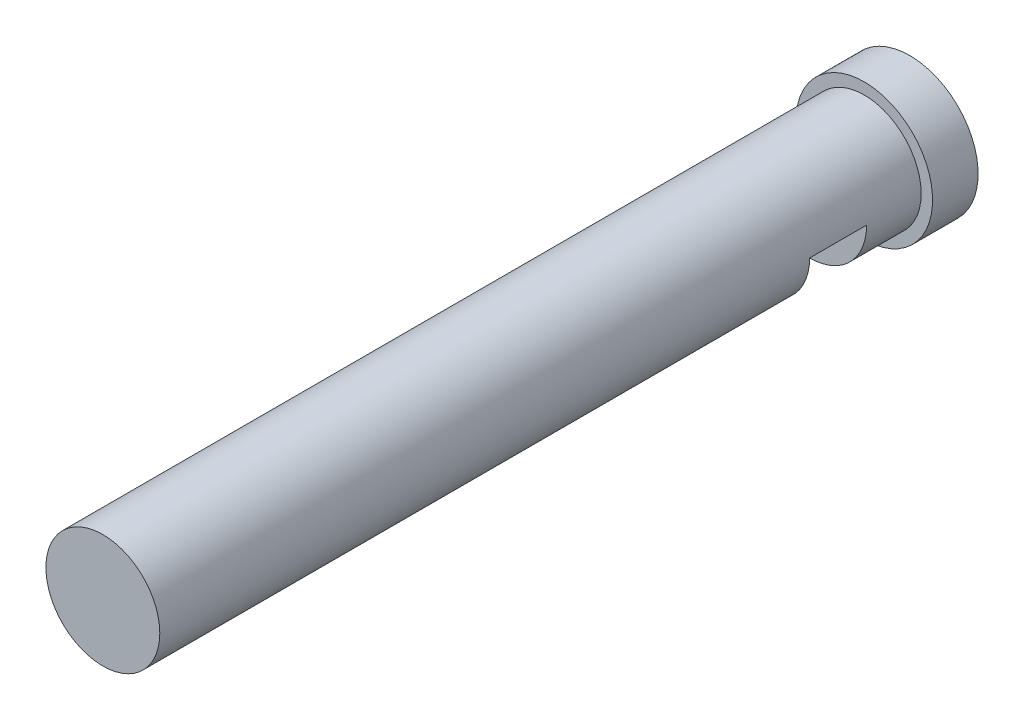
SolidWorks part; units mm, degrees
material "AISI 1020 Steel, Cold Rolled"
ref_plane "Front Plane" through (0, 0, 0) normal (0, 0, 1) x (1, 0, 0)
ref_plane "Top Plane" through (0, 0, 0) normal (0, 1, 0) x (1, 0, 0)
ref_plane "Right Plane" through (0, 0, 0) normal (1, 0, 0) x (0, 0, -1)
sketch "Sketch1" plane through (0, 0, 0) normal (0, 0, 1) x (1, 0, 0)
  circle A0 centre (0, 0) radius 6.35
  dimension "D1" = 12.7
extrude "Boss-Extrude1" add sketch "Sketch1" along normal blind 6.0833
sketch "Sketch4" plane through (0, 0, 0) normal (0, 0, -1) x (-1, 0, 0)
  circle A0 centre (0, 0) radius 7.62
  dimension "D1" = 15.24
extrude "Boss-Extrude2" add sketch "Sketch4" along normal blind 5.08
ref_plane "Plane6" through (0, 0, 3.175) normal (0, 0, -1) x (-1, 0, 0)
sketch "Sketch12" plane through (0, 0, 6.0833) normal (0, 0, 1) x (1, 0, 0)
  line L0 (0, -6.35) -> (6.35, 0)
  circle A0 centre (0, 0) radius 6.35 construction
  arc A1 (0, -6.35) -> (6.35, 0) centre (0, 0) cw
extrude "Boss-Extrude3" add sketch "Sketch12" along normal blind 6.35
sketch "Sketch13" plane through (0, 0, 12.4333) normal (0, 0, 1) x (1, 0, 0)
  circle A0 centre (0, 0) radius 6.35
extrude "Boss-Extrude4" add sketch "Sketch13" along normal blind 72.4611
